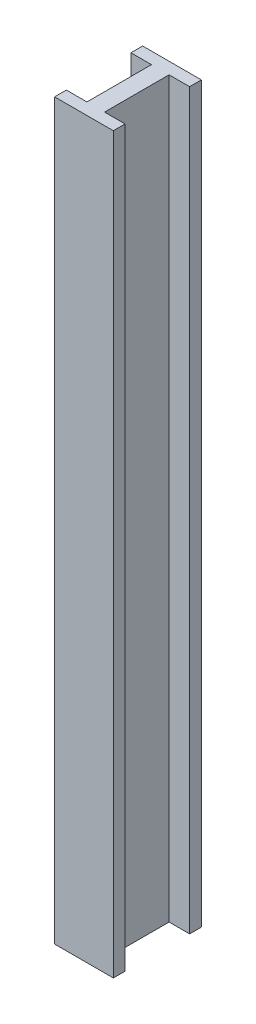
SolidWorks part; units mm, degrees
ref_plane "Front Plane" through (0, 0, 0) normal (0, 0, 1) x (1, 0, 0)
ref_plane "Top Plane" through (0, 0, 0) normal (0, 1, 0) x (1, 0, 0)
ref_plane "Right Plane" through (0, 0, 0) normal (1, 0, 0) x (0, 0, -1)
sketch "Sketch1" plane through (0, 0, 0) normal (0, 1, 0) x (1, 0, 0)
  line L0 (0, 0) -> (0, 44)
  line L1 (0, 44) -> (-14, 44)
  line L2 (-14, 44) -> (-14, 52)
  line L3 (-14, 52) -> (26, 52)
  line L4 (26, 52) -> (26, 44)
  line L5 (26, 44) -> (12, 44)
  line L6 (12, 44) -> (12, 0)
  line L7 (12, 0) -> (26, 0)
  line L8 (26, 0) -> (26, -8)
  line L9 (26, -8) -> (-14, -8)
  line L10 (-14, -8) -> (-14, 0)
  line L11 (-14, 0) -> (0, 0)
  dimension "D1" = 40
  dimension "D2" = 8
  dimension "D3" = 44
  dimension "D4" = 14
extrude "Boss-Extrude1" add sketch "Sketch1" along normal blind 500
